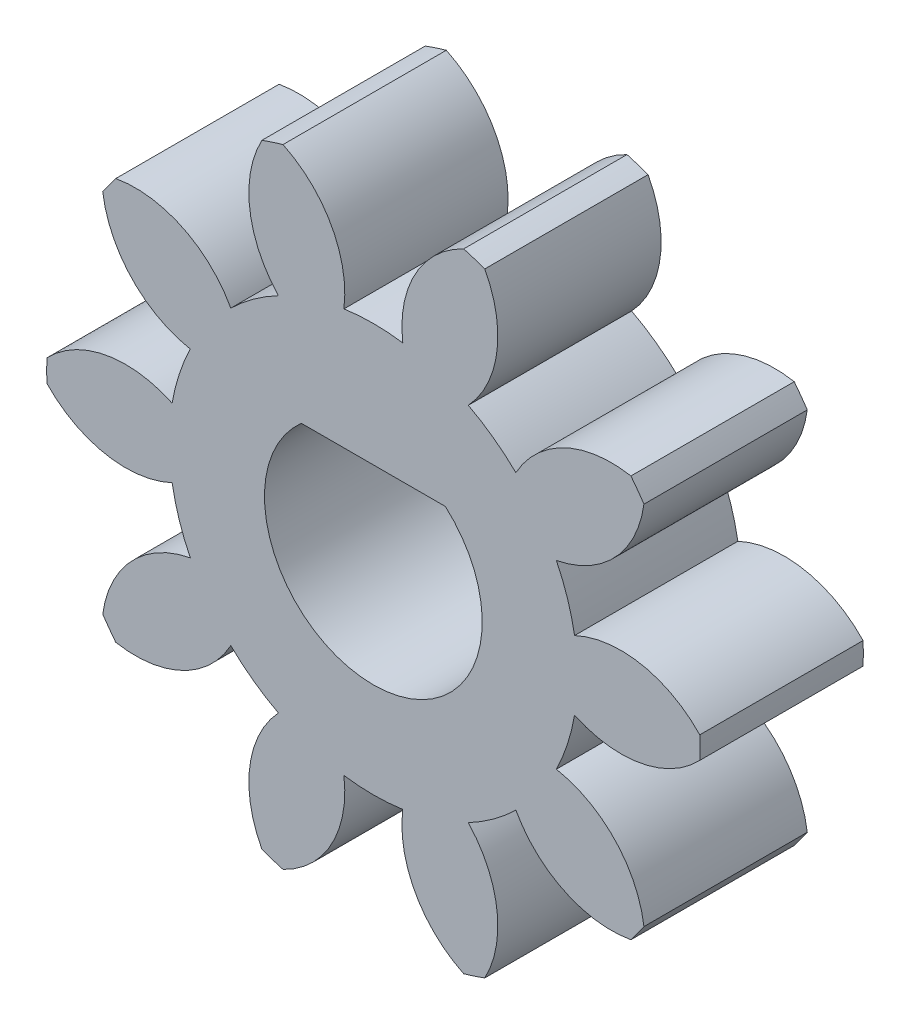
SolidWorks part; units mm, degrees
ref_plane "Front Plane" through (0, 0, 0) normal (0, 0, 1) x (1, 0, 0)
ref_plane "Top Plane" through (0, 0, 0) normal (0, 1, 0) x (1, 0, 0)
ref_plane "Right Plane" through (0, 0, 0) normal (1, 0, 0) x (0, 0, -1)
sketch "Sketch1" plane through (0, 0, 0) normal (0, 0, 1) x (1, 0, 0)
  circle A0 centre (0, 0) radius 6
  dimension "addendumDiameter" = 12
extrude "Boss-Extrude1" add sketch "Sketch1" along normal blind 3
sketch "Sketch2" plane through (0, 0, 3) normal (0, 0, 1) x (1, 0, 0)
  line L0 (0, 0) -> (0, 32.2263) construction
  line L1 (0, 0) -> (-6.6913, 20.5938) construction
  line L2 (-1.5259, 4.6963) -> (-0.7789, 4.939) construction
  circle A0 centre (0, 0) radius 3.75 construction
  circle A1 centre (0, 0) radius 4.6985 construction
  circle A2 centre (0, 0) radius 5 construction
  arc A3 (-1.6595, 5.7659) -> (-0.5404, 3.7109) centre (-2.5245, 3.9627) cw
  circle A4 centre (0, 0) radius 6 construction
  arc A5 (0.5404, 3.7109) -> (1.6595, 5.7659) centre (2.5245, 3.9627) cw
  arc A6 (-0.5404, 3.7109) -> (0.5404, 3.7109) centre (0, 0) cw
  arc A7 (-1.6595, 5.7659) -> (1.6595, 5.7659) centre (0, 0) cw
  dimension "dedendum circle" = 7.5
  dimension "base diameter" = 9.3969
  dimension "pitchDiameter" = 10
  dimension "D2" = 2
  dimension "D1" = 18
  dimension "D3" = 0.7854
extrude "Cut-Extrude1" cut sketch "Sketch2" against normal through all
pattern_circular "CirPattern1" count 10 over 360 about axis through (0, 0, 0) along (0, 0, 1) of "Cut-Extrude1"
sketch "Sketch4" [suppressed] plane through (0, 0, 3) normal (0, 0, 1) x (1, 0, 0)
  line L0 (0, 0) -> (0, 21.2521) construction
  line L3 (0, 0) -> (17.4265, 14.6226) construction
  line L4 (1.5677, 19.0606) -> (1.5677, 3.1277)
  line L5 (1.5677, 3.1277) -> (13.7196, 13.3244)
  line L6 (0, 0) -> (14.3062, 28.5426) construction
  arc A0 (13.7196, 13.3244) -> (1.5677, 19.0606) centre (0, 0) ccw
  arc A1 (8.9406, 18.5864) -> (7.83, 19.0809) centre (0, 0) ccw construction
  dimension "D3" = 3.4986
  dimension "D4" = 50
  dimension "D5" = 1.5
  dimension "D1" = 50
  dimension "D2" = 26.621
extrude "Cut-Extrude2" [suppressed] cut sketch "Sketch4" against normal through all contours L5 A0 L4
fillet "Fillet1" [suppressed] radius 0.75
pattern_circular "CirPattern2" [suppressed] count 6 over 360
fillet "Fillet2" [suppressed] radius 0.75
pattern_circular "CirPattern3" [suppressed] count 6 over 360
sketch "Sketch5" plane through (0, 0, 3) normal (0, 0, 1) x (1, 0, 0)
  line L0 (1.3229, 1.5) -> (-1.3229, 1.5)
  arc A0 (-1.3229, 1.5) -> (1.3229, 1.5) centre (0, 0) ccw
  dimension "D2" = 1.5
  dimension "D1" = 4
extrude "Cut-Extrude3" cut sketch "Sketch5" against normal through all
equation "\"module\"= 1.0"
equation "\"teeth\"= 10"
equation "\"pressureAngle\"= 20deg"
equation "\"gearThickness\"= 3"
equation "\"addendumFactor\"= 1"
equation "\"dedendumFactor\"= 1.25"
equation "\"pitch\"= 1 / \"module\""
equation "\"pitchDiameter\"= \"teeth\" / \"pitch\""
equation "\"addendum\"= \"addendumFactor\" / \"pitch\""
equation "\"dedendum\"= \"dedendumFactor\" / \"pitch\""
equation "\"D1@Boss-Extrude1\"=\"gearThickness\""
equation "\"addendumDiameter@Sketch1\"= \"pitchDiameter\" + 2 * \"addendum\""
equation "\"dedendum circle@Sketch2\"=\"pitchDiameter\" - 2 * \"dedendum\""
equation "\"base diameter@Sketch2\"=\"pitchDiameter\" * cos ( \"pressureAngle\" )"
equation "\"pitchDiameter@Sketch2\"=\"pitchDiameter\""
equation "\"D1@Sketch2\"=180/\"teeth\""
equation "\"D2@Sketch2\"=\"pitchDiameter\"/5"
equation "\"D3@Sketch2\"=PI/2/\"pitch\"/2"
equation "\"D1@CirPattern1\"=\"teeth\""
